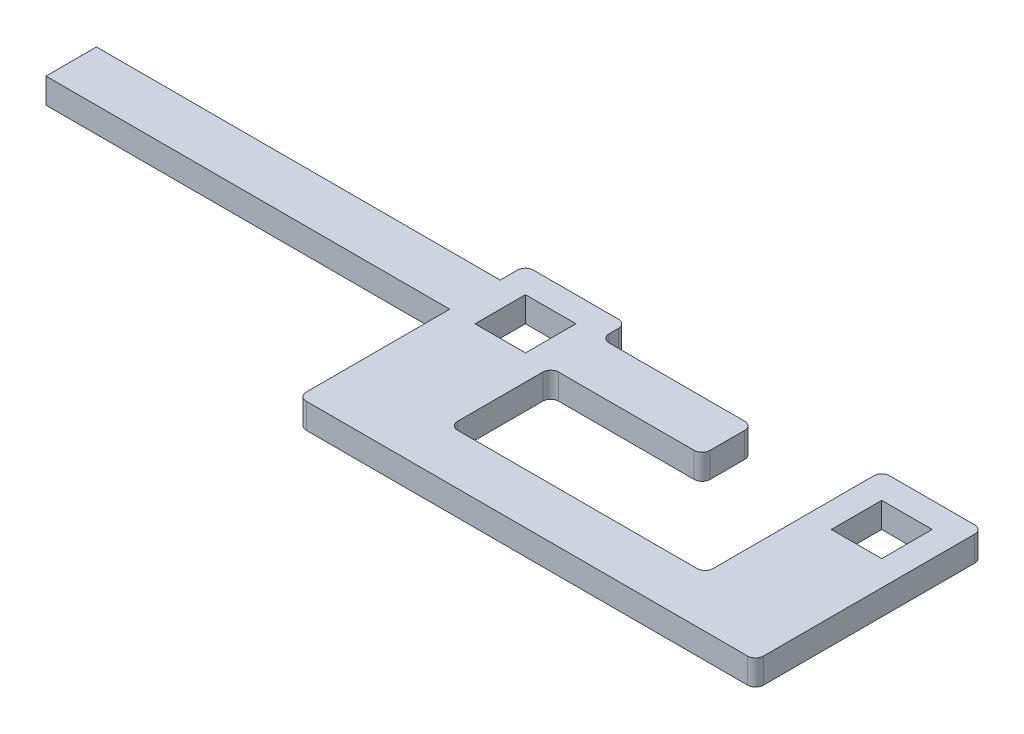
SolidWorks part; units mm, degrees
material "Beech"
ref_plane "Front Plane" through (0, 0, 0) normal (0, 0, 1) x (1, 0, 0)
ref_plane "Top Plane" through (0, 0, 0) normal (0, 1, 0) x (1, 0, 0)
ref_plane "Right Plane" through (0, 0, 0) normal (1, 0, 0) x (0, 0, -1)
sketch "Sketch1" plane through (0, 0, 0) normal (0, 1, 0) x (1, 0, 0)
  line L0 (0, 0) -> (0, 19.05)
  line L1 (0, 0) -> (19.05, 0)
  line L2 (0, 28.575) -> (12.7, 28.575)
  line L3 (12.7, 6.35) -> (12.7, 19.05)
  line L4 (44.825, 28.575) -> (44.825, 6.35)
  line L5 (44.825, 28.575) -> (57.525, 28.575)
  line L6 (42.65, 0) -> (57.525, 0)
  line L7 (57.525, 28.575) -> (57.525, 0)
  line L8 (12.7, 6.35) -> (44.825, 6.35)
  line L10 (12.7, 19.05) -> (31.75, 19.05)
  line L11 (19.05, 0) -> (42.65, 0)
  line L12 (3.175, 25.4) -> (3.175, 19.05)
  line L13 (3.175, 25.4) -> (9.525, 25.4)
  line L14 (3.175, 19.05) -> (9.525, 19.05)
  line L15 (9.525, 25.4) -> (9.525, 19.05)
  line L16 (48, 25.4) -> (48, 19.05)
  line L17 (48, 25.4) -> (54.35, 25.4)
  line L18 (48, 19.05) -> (54.35, 19.05)
  line L19 (54.35, 25.4) -> (54.35, 19.05)
  line L20 (0, 25.4) -> (-50.8, 25.4)
  line L21 (12.7, 25.4) -> (31.75, 25.4)
  line L22 (-50.8, 25.4) -> (-50.8, 19.05)
  line L23 (0, 19.05) -> (-50.8, 19.05)
  line L24 (0, 25.4) -> (0, 28.575)
  line L25 (31.75, 19.05) -> (31.75, 25.4)
  line L26 (12.7, 25.4) -> (12.7, 28.575)
  dimension "D1" = 6.35
  dimension "D2" = 6.35
  dimension "D3" = 6.35
  dimension "D4" = 6.35
  dimension "D5" = 44.825
  dimension "D6" = 3.175
  dimension "D7" = 19.05
  dimension "D8" = 3.175
  dimension "D9" = 3.175
  dimension "D10" = 3.175
  dimension "D11" = 3.175
  dimension "D12" = 3.175
  dimension "D13" = 19.05
  dimension "D14" = 50.8
  dimension "D15" = 6.35
  dimension "D16" = 6.35
  dimension "D17" = 19.05
extrude "Elastic_Extrude" add sketch "Sketch1" along normal blind 3.175
fillet "Elastic_CornerFillet" radius 1 12 edges at (12.7, 1.5875, -6.35) (44.825, 1.5875, -6.35) (44.825, 1.5875, -28.575) (57.525, 1.5875, -28.575) (57.525, 1.5875, 0) (0, 1.5875, 0) (0, 1.5875, -28.575) (12.7, 1.5875, -19.05) (31.75, 1.5875, -19.05) (31.75, 1.5875, -25.4) (12.7, 1.5875, -25.4) (12.7, 1.5875, -28.575)
equation "\"CageLeftBottomEdge\"=22.11mm"
equation "\"CageLeftTopEdge\"=22.11mm"
equation "\"CageRightBottomEdge\"=21.63mm"
equation "\"CageRightTopEdge\"=21.63mm"
equation "\"CageHeight\"=86.04mm"
equation "\"CageLength\"=73.76mm"
equation "\"CageTopScrewClearance\"=10mm"
equation "\"CageBottomScrewClearance\"=25mm"
equation "\"CageLeftTopDepth\"= 11.65mm"
equation "\"CageLeftBottomDepth\"=11.11mm"
equation "\"CageLeftTopHeight\"=8.56175mm"
equation "\"CageLeftBottomHeight\"=16mm"
equation "\"CageRightTopDepth\"= 11.05mm"
equation "\"CageRightBottomDepth\"=10.58mm"
equation "\"CageRightTopHeight\"=9.6mm"
equation "\"CageRightBottomHeight\"=15.49mm"
equation "\"CageLeftTopChannelDepth\"=2.41908mm"
equation "\"CageLeftBottomChannelDepth\"=2.588mm"
equation "\"CageLeftChannelHeight\"=11.7mm"
equation "\"CageRightTopChannelDepth\"=2.32mm"
equation "\"CageRightBottomChannelDepth\"=2.318mm"
equation "\"CageRightChannelHeight\"=10mm"
equation "\"CageChanRelHeight\"=23.99mm"
equation "\"CageChanRelDepth\"=5.492mm"
equation "\"CageChamberRadius\"=16.261mm"
equation "\"CageScrewDiameter\"=4.8mm"
equation "\"CageSetScrewDiameter\"=3.5mm"
equation "\"CageAxleRadius\"=6.639mm"
equation "\"CageAxleKeyHeight\"=1.619mm"
equation "\"CageAxleKeyWidth\"=2.662mm"
equation "\"CageHoseWindowWidth\"=16.29mm"
equation "\"CageHoseWindowHeight\"=26.5mm"
equation "\"CageHoseWindow-Edge\"=8.89mm"
equation "\"CageScrew-VerticalEdge\"=5.0mm"
equation "\"CageScrew-HorizontalEdge\"=7.5mm"
equation "\"CageScrew-HoseCornerScrewEdge\"=4.45mm"
equation "\"CageAxle-BottomEdge\"=56.05mm"
equation "\"CageAxle-FrontEdge\"=46.03mm"
equation "\"CageBackSetScrew-Axle\"=40mm"
equation "\"CageFrontSetScrew-Axle\"=22mm"
equation "\"CageVelocityWindow-BackEdge\"=34.8mm"
equation "\"CageVelocityWindow-BottomEdge\"=27.55mm"
equation "\"CageVelocityWindowHeight\"=22.29mm"
equation "\"CageVelocityWindowWidth\"=12.61mm"
equation "\"TriggerSlot-BottomEdge\"=6.35mm"
equation "\"TriggerSlot-FrontEdge\"=15mm"
equation "\"TriggerSlotSize\"=6.7mm"
equation "\"TriggerRackOffset\"=.236224in"
equation "\"TriggerSlotSizeInt\"=.25in"
equation "\"MotorMountLegLength\"=.25in"
equation "\"GearOffset\"=.264907in"
equation "\"TriggerSlotSpacing\"=.25in"
equation "\"TriggerMiniSlotWidth\"=3.5mm"
equation "\"TriggerRackWidth\"=6.5mm"
equation "\"whitemotordepth\"=11.27mm"
equation "\"whitemotorbackdepth\"=3.845mm"
equation "\"whitemotoraxledepth\" = 3.5mm"
equation "\"whitemotoraxleoffset\"=11.4mm"
equation "\"whitemotorwidth\"=12.07mm"
equation "\"whitemotorheight\"=16.68mm"
equation "\"whitemotorcylinderlength\" =13.04mm"
equation "\"whitemotorcylinderradius\"=3.845mm"
equation "\"whitemotorcylinderoffset\"=2.35mm"
equation "\"whitemotorcutoutlength\"=1.88mm"
equation "\"whitemotorouterrad\"=5mm"
equation "\"D4@Sketch1\"=\"elasticrackpegsize\""
equation "\"elasticrackpegspacing\"=1.76476378in"
equation "\"D5@Sketch1\"=\"elasticrackpegspacing\""
equation "\"D6@Sketch1\"=\"elasticrackpegbuffer\""
equation "\"elasticrackpegsize\"=.25in"
equation "\"D1@Sketch1\"=\"elasticrackpegsize\""
equation "\"D2@Sketch1\"=\"elasticrackpegsize\""
equation "\"D3@Sketch1\"=\"elasticrackpegsize\""
equation "\"elasticracklength\"=2in"
equation "\"D14@Sketch1\"=\"elasticracklength\""
equation "\"elasticrackpegbuffer\"=.125in"
equation "\"D11@Sketch1\"=\"elasticrackpegbuffer\""
equation "\"D12@Sketch1\"=\"elasticrackpegbuffer\""
equation "\"D10@Sketch1\"=\"elasticrackpegbuffer\""
equation "\"D9@Sketch1\"=\"elasticrackpegbuffer\""
equation "\"D8@Sketch1\"=\"elasticrackpegbuffer\""
equation "\"elasticbaybuffer\"=.25in"
equation "\"D15@Sketch1\"=\"elasticbaybuffer\""
equation "\"D16@Sketch1\"=\"elasticbaybuffer\""
equation "\"whitemotorinnerrad\"=2.95mm"
equation "\"elasticbaydepth\"=.75in"
equation "\"D7@Sketch1\"=\"elasticbaydepth\""
equation "\"D13@Sketch1\"=\"elasticbaydepth\""
equation "\"D17@Sketch1\"=\"elasticbaydepth\""
equation "\"elasticdepth\"=.125in"
equation "\"D1@Elastic_Extrude\"=\"elasticdepth\""
equation "\"motormountwidth\"=12mm"
equation "\"motormountcornerfillet\"=3mm"
equation "\"pandiscradius\"=14in"
equation "\"towermaterialwidth\"=.25in"
equation "\"towerslotlength\"=.5in"
equation "\"towermarkerspace\"=5in"
equation "\"towerslothorizoffset\"=1in"
equation "\"towerslothorizspacing\"=2in"
equation "\"towerslotvertoffset\"=3in"
equation "\"towerslotvertspacing\"=1in"
equation "\"towerheight\"=12in"
equation "\"towerupslot\"=1in"
equation "\"toweraxle\"=.5in"
equation "\"stepperouterrad\"=10mm"
equation "\"stepperscrewsize\"=3.45mm"
equation "\"stepperscrewc2c\"=49.5mm"
equation "\"stepperdepthoffset\"=24mm"
equation "\"stepperhorizoffset\"=22.91mm"
equation "\"shaftslotOD\"=18.8mm"
equation "\"shaftslotID\"=13.28mm"
equation "\"shaftkeywidth\"=2.67mm"
equation "\"shaftkeydepth\"=1.8mm"
equation "\"shaftcollartotaldepth\"=12.5mm"
equation "\"shaftsquaredepth\"=6mm"
equation "\"shaftsetscrewsize\"=3.5mm"
equation "\"shaftkeytightdepth\"=1.85mm"
equation "\"shaftslottightID\"=12.78mm"
equation "\"shaftsetscrewoffset\"=9mm"
equation "\"cagecollartotaldepth\"=10mm"
equation "\"cagecollartotalwidth\"=35mm"
equation "\"cagecollarbasedepth\"=4mm"
equation "\"gearhubintdiam\"=30mm"
equation "\"gearhubintwid\"=15mm"
equation "\"towerspeedwidth\"=2in"
equation "\"towerspeedheight\"=8in"
equation "\"towerspeedgap\"=2in"
equation "\"stepperaxleflat\"=.037in"
equation "\"stepperaxlerad\"=0.11811024in"
equation "\"ajaxaxlesize\"=3.87mm"
equation "\"ajaxinnercut\"=2.3mm"
equation "\"ajaxwidth\"=6.1mm"
equation "\"ajaxdiametral\"=25.8854"
equation "\"ajaxcutoutdepth\"=2.3mm"
equation "\"ajax4020gap\"=29.5mm"
equation "\"ajax4010gap\"=24.5mm"
equation "\"ajax20hubbuffer\"=0.240157in"
equation "\"ajax20hubholeoffset\"=.19685in"
equation "\"ajax20hubholesize\"=.059055in"
equation "\"ajax20cutoutint\"=13.4mm"
equation "\"ajax40hubholesize\"=7.21mm"
equation "\"ajax40hubholeoffset\"=10mm"
equation "\"ajax40hubbuffer\"=.350394in"
equation "\"ajax40cutoutint\"=32.6mm"
equation "\"bearingpandiscrad\"=6.8in"
equation "\"bearingpandiscang\"=48.75deg"
equation "\"bearingclearholedist\"=4.7345in"
equation "\"bearingclearholesize\"=.5in"
equation "\"bearingclearholeang\"=22.5deg"
equation "\"bearingmountholedist\"=4.25in"
equation "\"bearingwirehole\"=1.5in"
equation "\"no6diam\"=.146in"
equation "\"shortconangle\"=20deg"
equation "\"shortconlen\"=.875in"
equation "\"longconlen\"=1.25in"
equation "\"longconangle\"=15deg"
equation "\"TGMGearFaceDiameter\"=24.40mm"
equation "\"TGMCylinderLength\"=15.00mm"
equation "\"TGMScrewHole-Center\"=8.70mm"
equation "\"TGMScrewHoleDiameter\"=5.04mm"
equation "\"TGMCenterHoleDiameter\"=9.50mm"
equation "\"TGMShaftCollarSideLength\"=19.00mm"
equation "\"TGMShaftCollarDockingDepth\"=7.00mm"
equation "\"towerplatslotoffset\"=1.5in"
equation "\"towermotorpanelheight\"=10in"
equation "\"towerplatdepth\"=2in"
equation "\"ajaxhubdepth\"=.25in"
equation "\"shconangle\"=20deg"
equation "\"shconlen\"=1in"
equation "\"lnconlen\"=1.5in"
equation "\"lnconangle\"=15deg"
